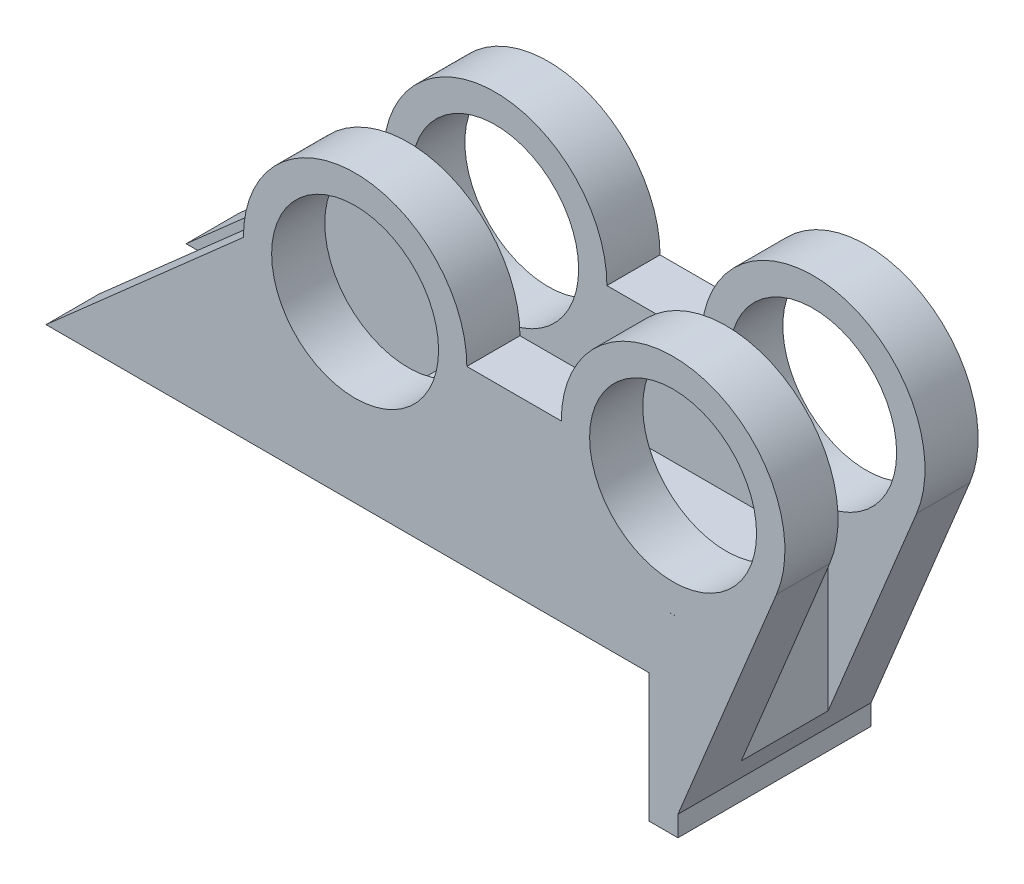
SolidWorks part; units mm, degrees
ref_plane "Front Plane" through (0, 0, 0) normal (0, 0, 1) x (1, 0, 0)
ref_plane "Top Plane" through (0, 0, 0) normal (0, 1, 0) x (1, 0, 0)
ref_plane "Right Plane" through (0, 0, 0) normal (1, 0, 0) x (0, 0, -1)
sketch "Sketch1" plane through (0, 0, 0) normal (0, 0, 1) x (1, 0, 0)
  line L0 (-5.3628, 17.0049) -> (33.3468, 17.0049)
  line L1 (33.3468, 17.0049) -> (33.3468, 0.1149)
  line L2 (33.3468, 0.1149) -> (37.1827, 0.1149)
  line L3 (37.1827, 0.1149) -> (37.1827, 25.2172)
  line L4 (37.1827, 25.2172) -> (-5.3628, 25.2172)
  line L5 (-5.3628, 25.2172) -> (-5.3628, 17.0049)
  line L6 (-5.2581, 39.9057) -> (36.5449, 39.9057) construction
  line L7 (37.1827, 2.8023) -> (50.1423, 34.3136)
  line L8 (9.4308, 39.9057) -> (21.8425, 39.9057)
  line L9 (-19.947, 39.9057) -> (-45.8916, 17.0049)
  line L10 (-45.8916, 17.0049) -> (-5.3628, 17.0049)
  circle A0 centre (-5.2581, 39.9057) radius 10.9728
  circle A1 centre (36.5449, 39.9057) radius 10.9728
  circle A2 centre (-5.2581, 39.9057) radius 14.6889
  circle A3 centre (36.5449, 39.9057) radius 14.7024
  dimension "D1" = 21.9456
  dimension "D2" = 21.9456
  dimension "D3" = 38.7096
extrude "Boss-Extrude1" add sketch "Sketch1" along normal blind 25.4
sketch "Sketch2" plane through (0, 0, 0) normal (1, 0, 0) x (0, 0, -1)
  line L0 (-18.415, 54.6081) -> (-6.985, 54.6081)
  line L1 (0, 54.6081) -> (-25.4, 54.6081) construction
  line L2 (-6.985, 54.6081) -> (-6.985, 24.2006)
  line L3 (-6.985, 24.2006) -> (-18.415, 24.2006)
  line L4 (-18.415, 24.2006) -> (-18.415, 54.6081)
  line L6 (-18.415, 54.6081) -> (-25.4, 54.6081)
  line L7 (-6.985, 54.6081) -> (0, 54.6081)
  line L8 (0, 34.3136) -> (0, 54.6081) construction
  line L9 (-25.4, 54.6081) -> (-25.4, 34.3136) construction
  dimension "D1" = 6.985
extrude "Cut-Extrude1" cut sketch "Sketch2" against normal mid plane 127 contours L4 L3 L2 L0
sketch "Sketch3" plane through (0, 24.2006, 0) normal (0, 1, 0) x (1, 0, 0)
  line L0 (-5.3628, -12.7) -> (45.9831, -12.7)
  line L2 (45.9831, -18.415) -> (45.9831, -6.985) construction
  line L4 (-37.7394, -6.985) -> (45.9831, -6.985) construction
  line L5 (-37.7394, -18.415) -> (45.9831, -18.415) construction
  line L6 (2.2367, -6.985) -> (2.2367, -18.415)
  point P2 (0, 0)
  point P15 (2.2367, -12.7)
  point P19 (16.2082, -12.7)
hole_wizard "CBORE for #8 Socket Head Cap Screw2" positions "3DSketch2" profile "Sketch5" counterbore size "#8" standard "ANSI Inch" end condition up to next
sketch3d "3DSketch2"
  point P0 (2.2367, 24.2006, 12.7)
  point P3 (16.2082, 24.2006, 12.7)
sketch "Sketch5" plane through (2.2367, 24.2006, 12.7) normal (1, 0, 0) x (0, 0, 1)
  line L0 (0, 0) -> (0, 7.1958)
  line L1 (0, 7.1958) -> (2.1526, 7.1958)
  line L3 (2.1526, 7.1958) -> (2.1527, 4.1656)
  line L4 (2.1527, 4.1656) -> (3.9687, 4.1656)
  line L5 (3.9687, 4.1656) -> (3.9687, 0)
  line L7 (3.9687, 0) -> (0, 0)
  line L11 (0, -6.35) -> (0, 107.95) construction
  dimension "Thru Hole Dia." = 4.3053
  dimension "Thru Hole Depth" = 7.1958
  dimension "C'Bore Dia." = 7.9375
  dimension "C'Bore Depth" = 4.1656
sketch "Sketch6" plane through (0, 24.2006, 0) normal (0, 1, 0) x (1, 0, 0)
  line L0 (45.9831, -18.415) -> (45.9831, -6.985) construction
  line L1 (45.9831, -18.4058) -> (38.5122, -18.4058)
  line L2 (45.9831, -18.4058) -> (45.9831, -6.985)
  line L3 (45.9831, -6.985) -> (38.5122, -6.985)
  line L4 (38.5122, -18.4058) -> (38.5122, -6.985)
  line L5 (-37.7394, -6.985) -> (45.9831, -6.985) construction
extrude "Cut-Extrude2" cut sketch "Sketch6" against normal mid plane 127
ref_plane "Plane1" through (-45.8916, 0, 0) normal (1, 0, 0) x (0, 0, -1)
sketch "Sketch9" plane through (-45.8916, 0, 0) normal (1, 0, 0) x (0, 0, -1)
  line L0 (-25.4, 17.0049) -> (0, 17.0049) construction
  line L1 (-18.415, 24.2006) -> (-6.985, 24.2006)
  line L2 (-18.415, 24.2006) -> (-18.415, 17.0049)
  line L3 (-18.415, 17.0049) -> (-6.985, 17.0049)
  line L4 (-6.985, 24.2006) -> (-6.985, 17.0049)
extrude "Cut-Extrude3" cut sketch "Sketch9" along normal blind 38.1
